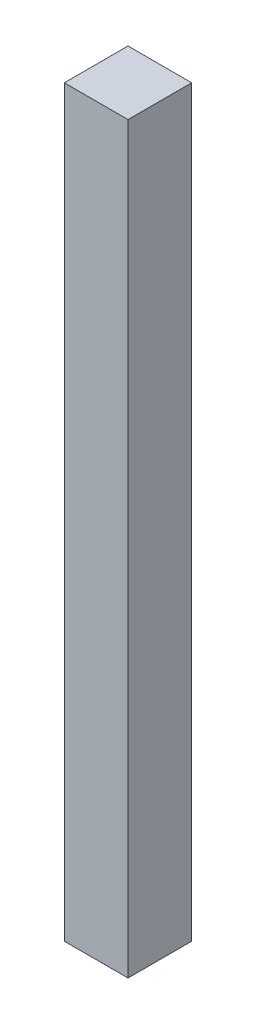
SolidWorks part; units mm, degrees
ref_plane "Front Plane" through (0, 0, 0) normal (0, 0, 1) x (1, 0, 0)
ref_plane "Top Plane" through (0, 0, 0) normal (0, 1, 0) x (1, 0, 0)
ref_plane "Right Plane" through (0, 0, 0) normal (1, 0, 0) x (0, 0, -1)
sketch "Sketch1" plane through (0, 0, 0) normal (0, 1, 0) x (1, 0, 0)
  line L1 (-88.9269, -53.2337) -> (-28.9269, -53.2337)
  line L2 (-88.9269, -53.2337) -> (-88.9269, 6.7663)
  line L3 (-88.9269, 6.7663) -> (-28.9269, 6.7663)
  line L4 (-28.9269, -53.2337) -> (-28.9269, 6.7663)
extrude "Boss-Extrude1" add sketch "Sketch1" against normal blind 700
